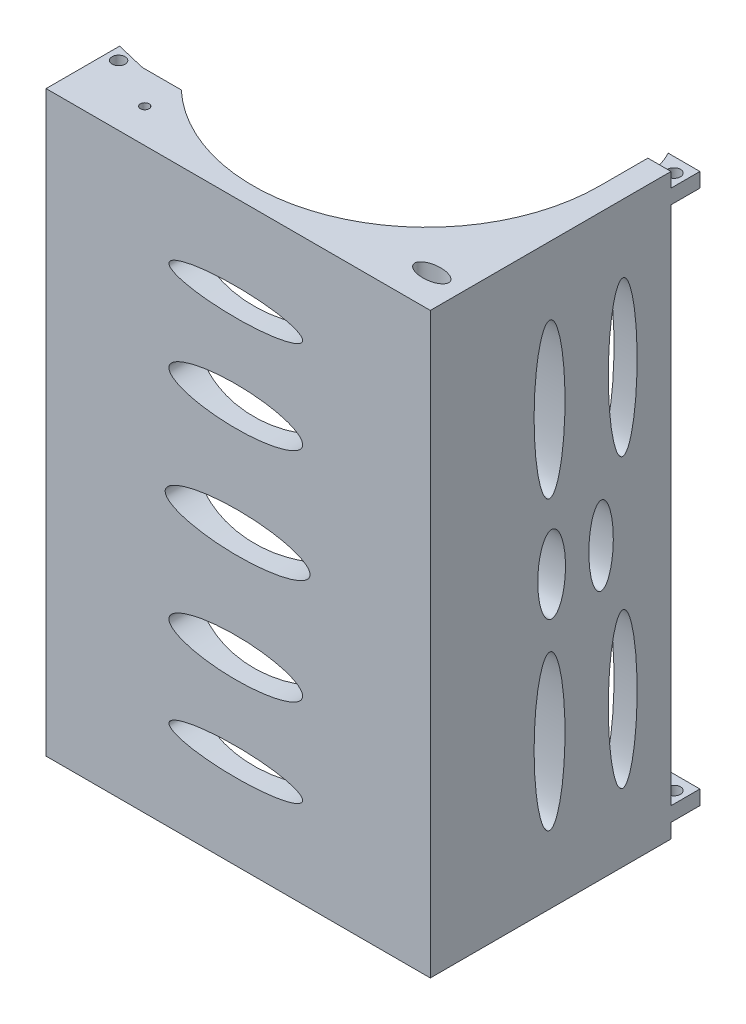
SolidWorks part; units mm, degrees
ref_plane "Front Plane" through (0, 0, 0) normal (0, 0, 1) x (1, 0, 0)
ref_plane "Top Plane" through (0, 0, 0) normal (0, 1, 0) x (1, 0, 0)
ref_plane "Right Plane" through (0, 0, 0) normal (1, 0, 0) x (0, 0, -1)
sketch "Sketch2" plane through (0, 0, 0) normal (0, 1, 0) x (1, 0, 0)
  line L0 (-91.2408, -7.8455) -> (36.7592, -7.8455)
  line L2 (-91.2408, 47.6545) -> (-91.2408, 163.7635) construction
  line L3 (36.7592, -7.8455) -> (41.6818, -7.8455)
  line L4 (-91.2408, -7.8455) -> (-91.2408, 47.6545)
  line L6 (33.6818, 105.4125) -> (41.6818, 105.4125)
  line L8 (33.6818, 88.8069) -> (33.6818, 105.4125)
  line L10 (41.6818, 105.4125) -> (41.6818, -7.8455)
  line L11 (-80.8104, 45.1317) -> (-67.4579, 45.1317)
  arc A0 (-91.2408, 47.6545) -> (-80.8104, 45.1317) centre (-23.0789, 306.6477) ccw
  arc A1 (-67.4579, 45.1317) -> (33.6818, 88.8069) centre (-26.3182, 88.8069) ccw
  point P3 (-86.0383, 46.3408)
  dimension "D2" = 120
  dimension "D1" = 55.5
extrude "Boss-Extrude1" add sketch "Sketch2" along normal blind 200
sketch "Sketch3" plane through (-91.2408, 0, 0) normal (-1, 0, 0) x (0, 0, 1)
  line L0 (7.8455, 200) -> (7.8455, 0) construction
  line L1 (7.8455, 194) -> (-22.1545, 194)
  line L2 (7.8455, 194) -> (7.8455, 6)
  line L3 (7.8455, 6) -> (-22.1545, 6)
  line L5 (-22.1545, 100) -> (7.8455, 100) construction
  line L7 (-47.6545, 200) -> (7.8455, 200) construction
  line L9 (-22.1545, 194) -> (-22.1545, 6)
  dimension "D1" = 6
  dimension "D2" = 30
extrude "Cut-Extrude1" cut sketch "Sketch3" against normal through all
ref_plane "Plane1" through (0, 195, 0) normal (0, 1, 0) x (1, 0, 0)
ref_plane "Plane2" through (0, 5, 0) normal (0, -1, 0) x (-1, 0, 0)
ref_plane "Plane3" through (0, 100, 0) normal (0, 1, 0) x (1, 0, 0)
ref_plane "Plane4" through (0, 190, 0) normal (0, 1, 0) x (1, 0, 0)
sketch "Sketch8" plane through (-91.2408, 0, 0) normal (-1, 0, 0) x (0, 0, 1)
  line L0 (-39.6545, 195) -> (-39.6545, 190)
  line L1 (73.1074, 195) -> (-73.1074, 195) construction
  line L2 (73.1074, 190) -> (-73.1074, 190) construction
  line L3 (-39.6545, 195) -> (-47.6545, 195)
  line L4 (-47.6545, 200) -> (-47.6545, 0) construction
  line L5 (-47.6545, 195) -> (-47.6545, 190)
  line L6 (-47.6545, 190) -> (-39.6545, 190)
  dimension "D1" = 8
extrude "Cut-Extrude2" cut sketch "Sketch8" against normal blind 8
mirror "Mirror2" about plane through (0, 100, 0) normal (0, 1, 0) of "Cut-Extrude2"
sketch "Sketch9" plane through (0, 200, 0) normal (0, 1, 0) x (1, 0, 0)
  circle A0 centre (-87.1256, 43.1305) radius 2.25
  dimension "D1" = 4.5
extrude "Cut-Extrude3" cut sketch "Sketch9" against normal blind 20
mirror "Mirror3" about plane through (0, 100, 0) normal (0, 1, 0) of "Cut-Extrude3"
sketch "Sketch11" plane through (0, 200, 0) normal (0, 1, 0) x (1, 0, 0)
  circle A0 centre (-68.8658, 16.2918) radius 1.5
  dimension "D1" = 3
extrude "Cut-Extrude5" cut sketch "Sketch11" against normal blind 227
sketch "Sketch13" plane through (0, 0, 0) normal (0, -1, 0) x (1, 0, 0)
  line L0 (-91.2408, 7.8455) -> (41.6818, 7.8455) construction
  line L1 (-74.8617, 7.8455) -> (36.6024, 7.8455)
  line L2 (-74.8617, 7.8455) -> (-74.8617, -6.1128)
  line L3 (-74.8617, -6.1128) -> (-56.4408, -6.1128)
  line L4 (36.6024, 7.8455) -> (36.6024, -6.1128)
  line L11 (36.6024, -22.1545) -> (36.6024, -6.1128)
  line L12 (-56.4408, -6.1128) -> (-56.4408, -22.1545)
  line L19 (-56.4408, -22.1545) -> (36.6024, -22.1545)
  line L20 (41.6818, -22.1545) -> (-91.2408, -22.1545) construction
extrude "Cut-Extrude7" cut sketch "Sketch13" against normal blind 258
sketch "Sketch15" plane through (0, 200, 0) normal (0, 1, 0) x (1, 0, 0)
  line L7 (36.6024, 22.1545) -> (36.6024, -7.8455)
  line L9 (-67.4579, 45.1317) -> (-80.8104, 45.1317)
  line L10 (-67.4579, 45.1317) -> (-80.8104, 45.1317)
  line L11 (-56.4408, 6.1128) -> (-56.4408, 22.1545)
  line L12 (-56.4408, 6.1128) -> (-56.4408, 22.1545)
  line L13 (-74.8617, -7.8455) -> (-74.8617, 6.1128)
  line L14 (-74.8617, 6.1128) -> (-56.4408, 6.1128)
  line L21 (36.6024, 22.1545) -> (36.6024, -7.8455)
  line L22 (36.6024, -7.8455) -> (41.6818, -7.8455)
  line L23 (36.6024, -7.8455) -> (41.6818, -7.8455)
  line L24 (-91.2408, 47.6545) -> (-91.2408, -7.8455)
  line L25 (-91.2408, -7.8455) -> (-74.8617, -7.8455)
  line L26 (-74.8617, -7.8455) -> (-74.8617, 6.1128)
  line L27 (-74.8617, 6.1128) -> (-56.4408, 6.1128)
  line L37 (-91.2408, 47.6545) -> (-91.2408, -7.8455)
  line L38 (-91.2408, -7.8455) -> (-74.8617, -7.8455)
  line L39 (-56.4408, 22.1545) -> (36.6024, 22.1545)
  line L40 (-56.4408, 22.1545) -> (36.6024, 22.1545)
  line L41 (41.6818, -7.8455) -> (41.6818, 105.4125)
  line L42 (41.6818, -7.8455) -> (41.6818, 105.4125)
  line L43 (41.6818, 105.4125) -> (33.6818, 105.4125)
  line L45 (33.6818, 105.4125) -> (33.6818, 88.8069)
  line L46 (33.6818, 105.4125) -> (33.6818, 88.8069)
  line L47 (41.6818, 105.4125) -> (33.6818, 105.4125)
  circle A0 centre (-87.1256, 43.1305) radius 2.25 construction
  arc A1 (-91.2408, 47.6545) -> (-80.8104, 45.1317) centre (-23.0789, 306.6477) ccw
  arc A2 (-91.2408, 47.6545) -> (-80.8104, 45.1317) centre (-23.0789, 306.6477) ccw
  circle A3 centre (-87.1256, 43.1305) radius 2.25
  circle A4 centre (-68.8658, 16.2918) radius 1.5 construction
  circle A5 centre (-68.8658, 16.2918) radius 1.5
  arc A8 (-67.4579, 45.1317) -> (33.6818, 88.8069) centre (-26.3182, 88.8069) ccw
  arc A9 (-67.4579, 45.1317) -> (33.6818, 88.8069) centre (-26.3182, 88.8069) ccw
  dimension "D1" = 0
sketch "Sketch16" plane through (41.6818, 0, 0) normal (1, 0, 0) x (0, 0, -1)
  ellipse E0 centre (88.7022, 149.7202) end of major axis (88.7022, 176.4515) minor radius 4.9898
  ellipse E1 centre (63.3966, 149.7202) end of major axis (63.3966, 176.4515) minor radius 5.3463
extrude "Cut-Extrude8" cut sketch "Sketch16" against normal blind 20
mirror "Mirror4" about plane through (0, 100, 0) normal (0, 1, 0) of "Cut-Extrude8"
sketch "Sketch17" plane through (0, 195, 0) normal (0, 1, 0) x (1, 0, 0)
  line L0 (-91.2408, 47.6545) -> (-91.2408, -7.8455) construction
  line L1 (-91.2408, 22.1545) -> (41.6818, 22.1545)
  line L2 (-91.2408, 22.1545) -> (-91.2408, -7.8455)
  line L3 (-91.2408, -7.8455) -> (41.6818, -7.8455)
  line L4 (41.6818, 22.1545) -> (41.6818, -7.8455)
  dimension "D1" = 30
extrude "Cut-Extrude9" cut sketch "Sketch17" against normal through all and the other way through all
sketch "Sketch18" plane through (0, 195, 0) normal (0, 1, 0) x (1, 0, 0)
  line L0 (30.7176, 115.4125) -> (33.6818, 115.4125)
  line L1 (41.6818, 105.4125) -> (33.6818, 105.4125)
  line L2 (41.6818, 105.4125) -> (41.6818, 115.4125)
  line L3 (41.6818, 115.4125) -> (33.6818, 115.4125)
  circle A1 centre (37.6818, 110.447) radius 2.25
  arc A2 (33.6818, 105.4125) -> (30.7176, 115.4125) centre (7.6805, 103.1447) ccw
  dimension "D3" = 4.5
  dimension "D1" = 8
  dimension "D2" = 10
extrude "Boss-Extrude2" add sketch "Sketch18" against normal blind 5
mirror "Mirror5" about plane through (0, 100, 0) normal (0, 1, 0) of "Boss-Extrude2"
sketch "Sketch20" plane through (0, 200, 0) normal (0, 1, 0) x (1, 0, 0)
  circle A0 centre (-68.8658, 33.9117) radius 1.5
  dimension "D1" = 3
extrude "Cut-Extrude10" cut sketch "Sketch20" against normal blind 15
mirror "Mirror6" about plane through (0, 100, 0) normal (0, 1, 0) of "Cut-Extrude10"
sketch "Sketch21" plane through (0, 0, -22.1545) normal (0, 0, 1) x (1, 0, 0)
  ellipse E0 centre (-25.628, 168.8867) end of major axis (-48.7585, 168.8867) minor radius 4.7692
  ellipse E1 centre (-25.628, 137.6487) end of major axis (-48.7585, 137.6487) minor radius 6.6768
extrude "Cut-Extrude11" cut sketch "Sketch21" against normal blind 50
mirror "Mirror7" about plane through (0, 100, 0) normal (0, 1, 0) of "Cut-Extrude11"
sketch "Sketch23" plane through (0, 0, -22.1545) normal (0, 0, 1) x (1, 0, 0)
  line L0 (45.7919, 100) -> (-45.7919, 100) construction
  ellipse E0 centre (-24.9893, 100) end of major axis (-50.0394, 100) minor radius 6.9061
extrude "Cut-Extrude12" cut sketch "Sketch23" against normal blind 40
sketch "Sketch24" plane through (41.6818, 0, 0) normal (1, 0, 0) x (0, 0, -1)
  line L0 (45.7919, 100) -> (-45.7919, 100) construction
  ellipse E0 centre (81.2184, 100) end of major axis (81.2184, 113.6203) minor radius 4.234
  ellipse E1 centre (64.1127, 100) end of major axis (64.1127, 113.3991) minor radius 4.7983
extrude "Cut-Extrude13" cut sketch "Sketch24" against normal blind 40
sketch "Sketch25" plane through (-91.2408, 0, 0) normal (-1, 0, 0) x (0, 0, 1)
  line L0 (45.7919, 100) -> (-45.7919, 100) construction
  ellipse E0 centre (-35.5754, 100) end of major axis (-35.5754, 146.1893) minor radius 4.7404
extrude "Cut-Extrude14" cut sketch "Sketch25" against normal blind 20
sketch "Sketch26" plane through (0, 200, 0) normal (0, 1, 0) x (1, 0, 0)
  ellipse E0 centre (30.6713, 33.6572) end of major axis (24.7866, 33.6572) minor radius 3.0513
extrude "Cut-Extrude15" cut sketch "Sketch26" against normal through all
